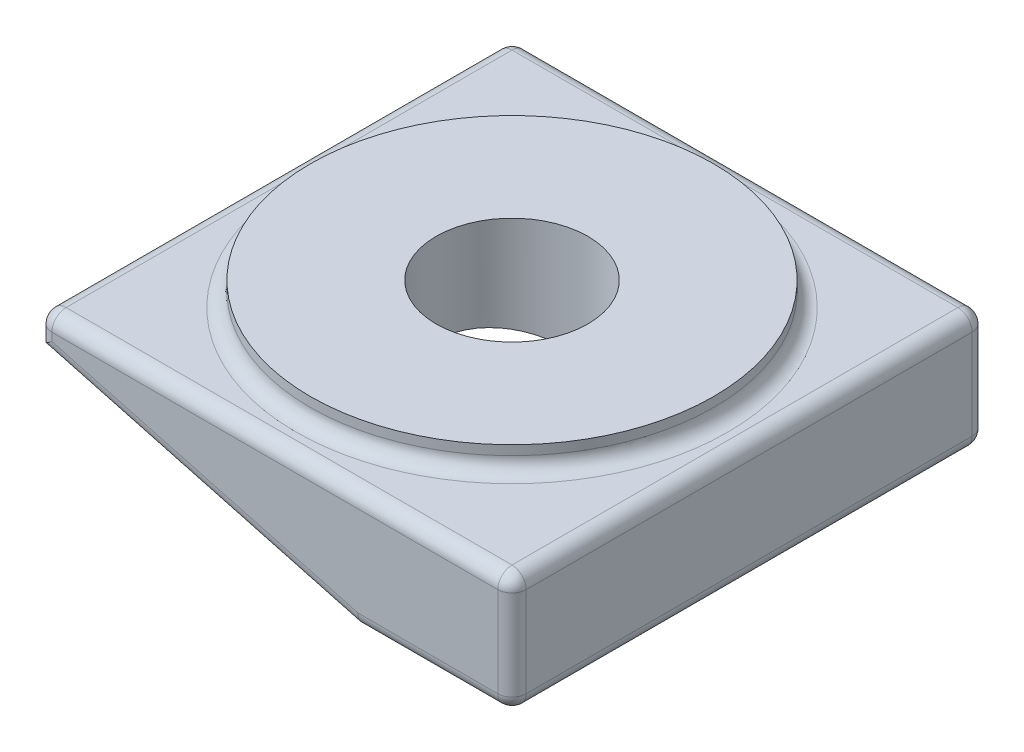
SolidWorks part; units mm, degrees
material "Gray Cast Iron"
ref_plane "Front Plane" through (0, 0, 0) normal (0, 0, 1) x (1, 0, 0)
ref_plane "Top Plane" through (0, 0, 0) normal (0, 1, 0) x (1, 0, 0)
ref_plane "Right Plane" through (0, 0, 0) normal (1, 0, 0) x (0, 0, -1)
sketch "Sketch2" plane through (0, 0, 0) normal (0, 0, 1) x (1, 0, 0)
  line L0 (0, 0) -> (0, 25)
  line L1 (0, 25) -> (-100, 25)
  line L2 (-100, 25) -> (-100, 18)
  line L3 (-100, 18) -> (-32.8231, 0)
  line L4 (-32.8231, 0) -> (0, 0)
  dimension "D1" = 100
  dimension "D2" = 25
  dimension "D3" = 7
  dimension "D4" = 15
extrude "Boss-Extrude1" add sketch "Sketch2" along normal mid plane 100
sketch "Sketch3" plane through (0, 25, 0) normal (0, 1, 0) x (1, 0, 0)
  line L0 (0, -50) -> (0, 50) construction
  line L1 (0, -50) -> (-100, -50) construction
  circle A0 centre (-50, 0) radius 42.5
  circle A1 centre (-50, 0) radius 16
  dimension "D1" = 85
  dimension "D2" = 32
  dimension "D3" = 50
  dimension "D4" = 50
extrude "Boss-Extrude2" add sketch "Sketch3" along normal blind 5
sketch "Sketch4" plane through (0, 25, 0) normal (0, 1, 0) x (1, 0, 0)
  circle A0 centre (-50, 0) radius 16
extrude "Cut-Extrude1" cut sketch "Sketch4" against normal through all
sketch "Sketch6" plane through (-2.1987, -8.2058, 0) normal (-0.2588, -0.9659, 0) x (0.9659, -0.2588, 0)
  line L1 (-112.9587, 46) -> (-12.9139, 46)
  line L2 (-112.9587, 46) -> (-112.9587, -46)
  line L3 (-112.9587, -46) -> (-12.9139, -46)
  line L4 (-12.9139, 46) -> (-12.9139, -46)
  dimension "D1" = 92
  dimension "D2" = 4
extrude "Cut-Extrude3" cut sketch "Sketch6" against normal blind 2
fillet "Fillet1" radius 3 14 edges at (-100, 21.5, 50) (-100, 25, 0) (-100, 21.5, -50) (-50, 25, -50) (-66.4115, 9, -50) (-16.4115, 0, -50) (0, 12.5, -50) (0, 0, 0) (0, 12.5, 50) (-16.4115, 0, 50) (-66.4115, 9, 50) (0, 25, 0) (-50, 25, 50) (-7.5, 25, 0)
